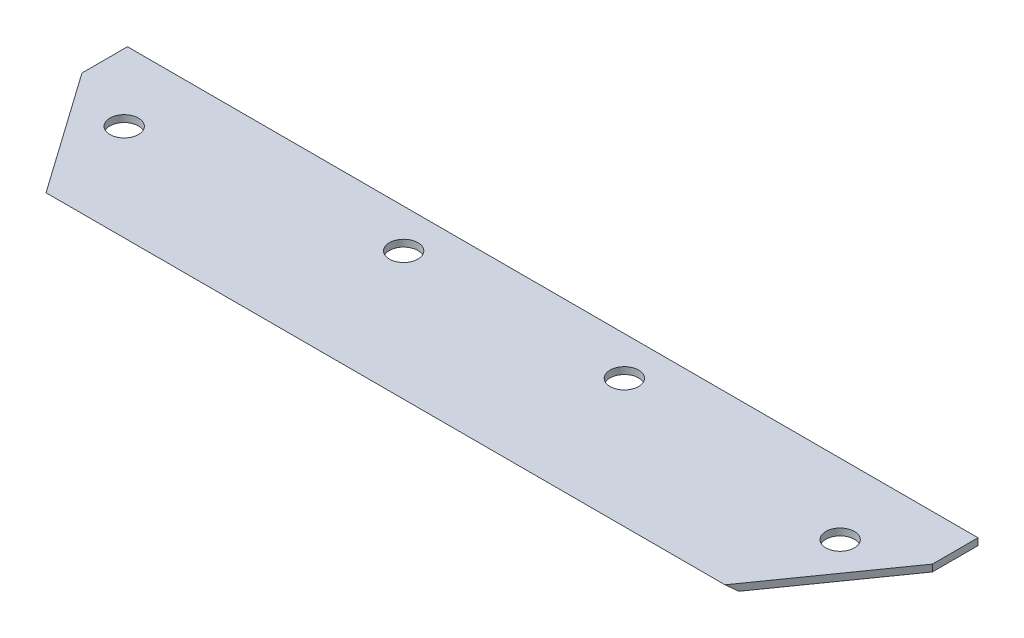
SolidWorks part; units mm, degrees
material "Ti-6Al-4VSolution treated and aged (SS)"
ref_plane "Front Plane" through (0, 0, 0) normal (0, 0, 1) x (1, 0, 0)
ref_plane "Top Plane" through (0, 0, 0) normal (0, 1, 0) x (1, 0, 0)
ref_plane "Right Plane" through (0, 0, 0) normal (1, 0, 0) x (0, 0, -1)
sketch "Sketch1" plane through (0, 0, 0) normal (0, 1, 0) x (1, 0, 0)
  line L1 (-79, -21.75) -> (79, -21.75)
  line L2 (-79, -21.75) -> (-79, 21.75)
  line L3 (-79, 21.75) -> (79, 21.75)
  line L4 (79, -21.75) -> (79, 21.75)
  line L5 (-79, -21.75) -> (79, 21.75) construction
  line L6 (-79, 21.75) -> (79, -21.75) construction
  point P0 (0, 0)
  dimension "D1" = 43.5
  dimension "D2" = 158
extrude "Boss-Extrude1" add sketch "Sketch1" along normal blind 1.27
sketch "Sketch2" plane through (79, 0, 0) normal (1, 0, 0) x (0, 0, -1)
  line L0 (-22.5856, 12.4042) -> (-22.5856, -1.6208)
  line L1 (-5.8712, -1.6208) -> (-22.5856, 12.4042)
  line L3 (25.439, -25.2824) -> (7.3812, -10.13) construction
  line L5 (-22.5856, -1.6208) -> (-5.8712, -1.6208)
  dimension "D1" = 2
extrude "Cut-Extrude1" cut sketch "Sketch2" against normal through all
hole_wizard "M5 Clearance Hole1" positions "Sketch4" profile "Sketch3" hole size "M5" standard "ANSI Metric" end condition through all
sketch "Sketch4" plane through (0, 1.27, 0) normal (0, 1, 0) x (1, 0, 0)
  circle A0 centre (-66.5, 8.6392) radius 2.1 construction
  circle A1 centre (-20.5, 14.5554) radius 2.1 construction
  circle A2 centre (20.5, 14.5554) radius 2.1 construction
  circle A3 centre (66.5, 8.6392) radius 2.1 construction
  point P0 (-66.5, 8.6392)
  point P2 (-20.5, 14.5554)
  point P4 (20.5, 14.5554)
  point P6 (66.5, 8.6392)
sketch "Sketch3" plane through (-66.5, 1.27, -8.6392) normal (1, 0, 0) x (0, 0, 1)
  line L0 (0, 0) -> (0, 1.27)
  line L1 (0, 1.27) -> (2.65, 1.27)
  line L2 (2.65, 1.27) -> (2.65, 0)
  line L5 (2.65, 0) -> (0, 0)
  line L11 (0, -6.35) -> (0, 107.95) construction
  dimension "Thru Hole Dia." = 5.3
  dimension "Thru Hole Depth" = 1.27
sketch "Sketch5" plane through (0, 0, 0) normal (0, -1, 0) x (1, 0, 0)
  line L2 (-79, -13.2888) -> (-64.1366, 7.8028)
  line L3 (-79, -21.75) -> (-79, 7.8028) construction
  line L4 (-79, 7.8028) -> (79, 7.8028) construction
  line L5 (-79, -13.2888) -> (-79, 13.928)
  line L6 (-79, 13.928) -> (-59.8201, 13.928)
  line L7 (-64.1366, 7.8028) -> (-59.8201, 13.928)
  line L8 (0, 0) -> (0, 42.1687) construction
  line L9 (64.1366, 7.8028) -> (59.8201, 13.928)
  line L10 (79, 13.928) -> (59.8201, 13.928)
  line L11 (79, -13.2888) -> (79, 13.928)
  line L12 (79, -13.2888) -> (64.1366, 7.8028)
  ellipse E1 centre (0, -97.9217) end of major axis (0, -231.3307) minor radius 102.1972 (-68.1188, 1.5301) -> (-80.5, -15.7328) ccw construction
extrude "Cut-Extrude2" cut sketch "Sketch5" against normal through all
